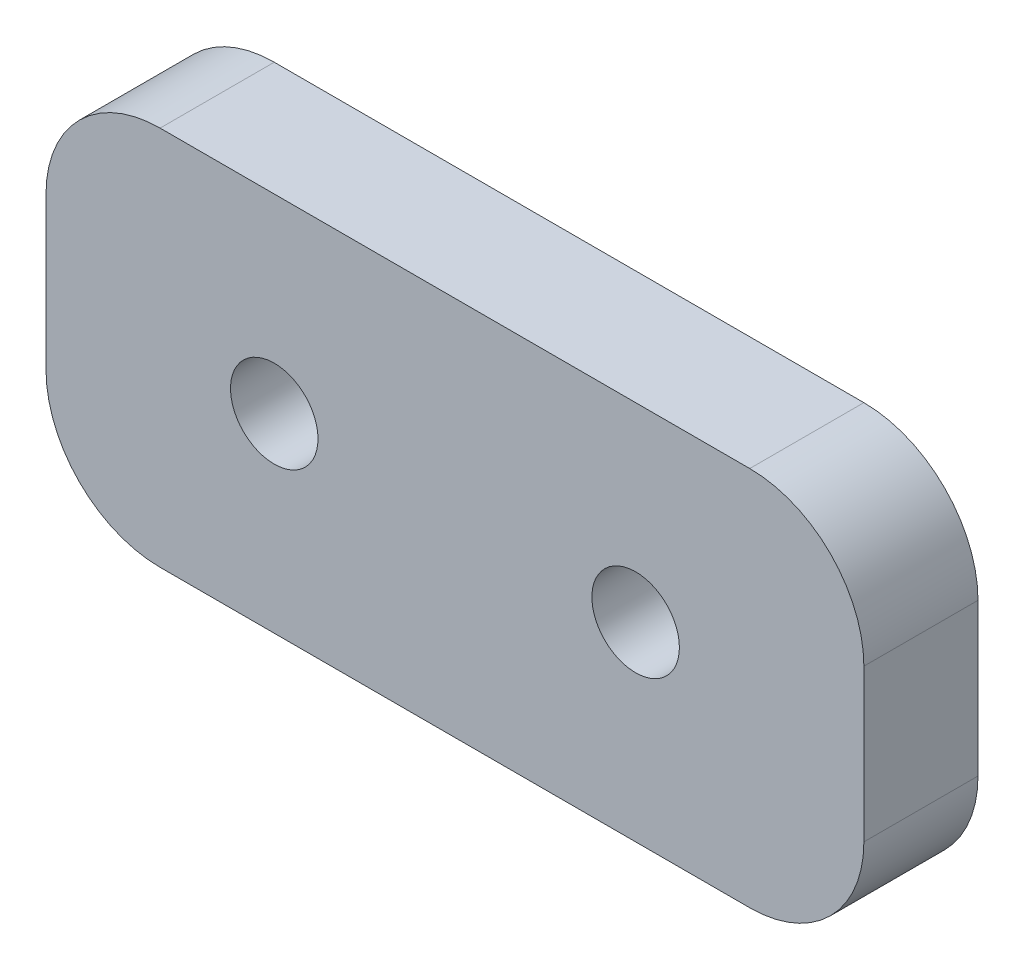
SolidWorks part; units mm, degrees
material "A-玻璃纤维"
ref_plane "前视基准面" through (0, 0, 0) normal (0, 0, 1) x (1, 0, 0)
ref_plane "上视基准面" through (0, 0, 0) normal (0, 1, 0) x (1, 0, 0)
ref_plane "右视基准面" through (0, 0, 0) normal (1, 0, 0) x (0, 0, -1)
sketch "草图1" plane through (0, 0, 0) normal (0, 0, 1) x (1, 0, 0)
  line L1 (0, 0) -> (21.5, 0)
  line L2 (0, 0) -> (0, 10)
  line L3 (0, 10) -> (21.5, 10)
  line L4 (21.5, 0) -> (21.5, 10)
  circle A0 centre (6, 5) radius 1.15
  circle A1 centre (15.5, 5) radius 1.15
  dimension "D1" = 9.5
  dimension "D2" = 2.3
  dimension "D3" = 6
  dimension "D4" = 6
  dimension "D5" = 5
  dimension "D6" = 10
extrude "凸台-拉伸1" add sketch "草图1" along normal blind 3
fillet "圆角1" radius 3 4 edges at (0, 10, 1.5) (21.5, 10, 1.5) (21.5, 0, 1.5) (0, 0, 1.5)
